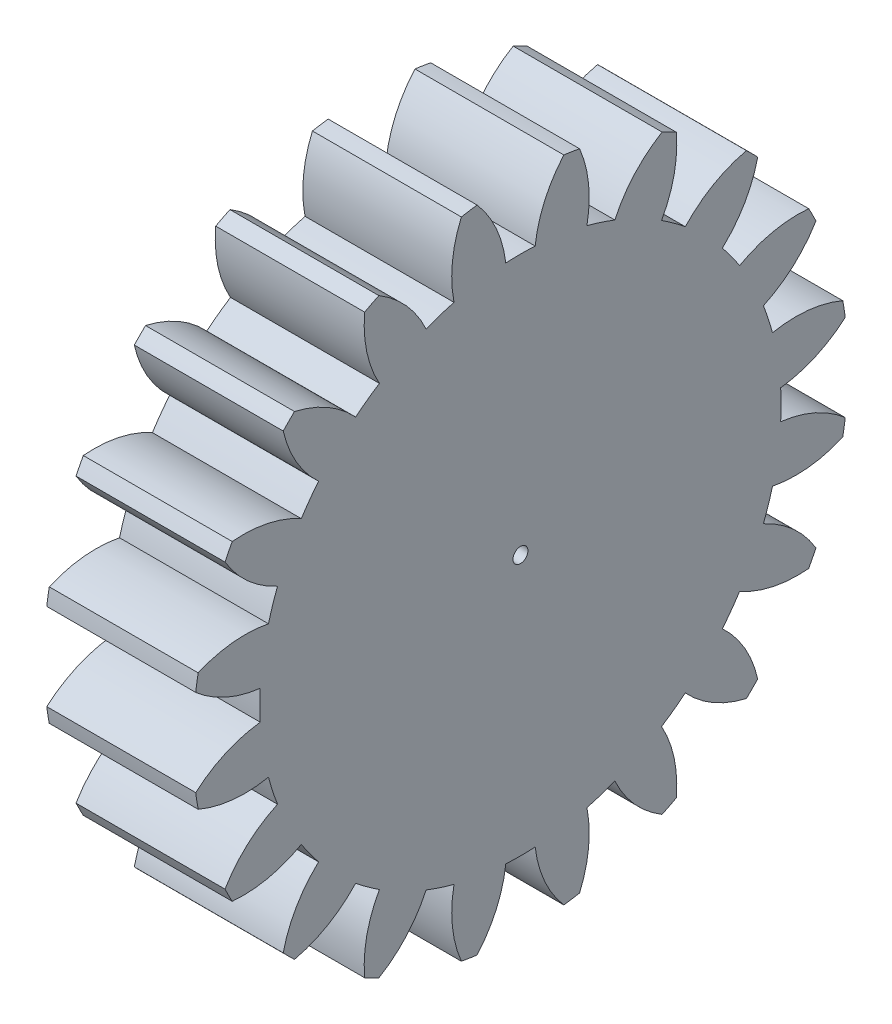
SolidWorks part; units mm, degrees
ref_plane "Plane1" through (0, 0, 0) normal (0, 0, 1) x (1, 0, 0)
ref_plane "Plane2" through (0, 0, 0) normal (0, 1, 0) x (1, 0, 0)
ref_plane "Plane3" through (0, 0, 0) normal (1, 0, 0) x (0, 0, -1)
other "Configuration Table"
sketch "HoldingSke" plane through (0, 0, 0) normal (0, 1, 0) x (1, 0, 0)
  line L0 (0, 0) -> (0.4698, -0.171)
  line L1 (-15, 0) -> (100, 0) construction
  line L2 (0, 0) -> (-2.1039, 2.3779)
  line L3 (0, 0) -> (-11.863, 4.5341)
  line L4 (0, 0) -> (8.1152, 2.9537)
  line L5 (0, 0) -> (-46.8476, -17.4728)
  line L6 (0, 0) -> (-8.2896, -5.593)
  line L7 (-2.1039, 2.3779) -> (8.6586, 51.2059)
  line L8 (-76.2, 54.61) -> (-76.1, 54.61)
  line L9 (-71.009, 38.7566) -> (-53.1078, 45.2721)
  line L10 (-76.2, 71.12) -> (104.1128, 71.12)
  line L11 (0, 0) -> (-10, 0)
  line L12 (-76.2, 101.6) -> (-76.133, 101.6)
  line L13 (24.9733, 27.94) -> (52.9518, 28.4284)
  line L14 (24.9733, 27.94) -> (24.9743, 27.94)
  line L15 (24.9733, 27.94) -> (100.4006, 29.5858)
  line L16 (-63.627, -2) -> (-12.827, -2)
  circle A0 centre (0, 0) radius 0.5
  circle A1 centre (0, 0) radius 17.499
  circle A2 centre (0, 0) radius 37.5
  circle A3 centre (0, 0) radius 0.5
  dimension "MHD" = 34.998
  dimension "Hub_dia" = 75
  dimension "Bore" = 1
  dimension "MBD" = 1
  dimension "Num_teeth" = 20
  dimension "Pitch" = 0.5
  dimension "Overall_len" = 50
  dimension "Show_teeth" = 20
  dimension "Thickness" = 10
  dimension "OAL" = 50.0001
  dimension "T_dim" = 0.1
  dimension "Ap" = 20
  dimension "H" = 19.05
  dimension "Pitch_radius" = 180.3128
  dimension "Width" = 10
  dimension "Backlash" = 0.067
  dimension "Addendum_fac" = 1
  dimension "Dedendum_fac" = 1.25
  dimension "Clearance_fac" = 0.25
  dimension "Dedendum_add" = 0.001
  dimension "Module" = 2
sketch "BasProSke" plane through (0, 0, 0) normal (0, 1, 0) x (1, 0, 0)
  line L0 (-10, 0) -> (60, 0) construction
  line L1 (0, 0) -> (0, 22)
  line L2 (0, 0) -> (10, 0)
  line L3 (10, 0) -> (10, 22)
  line L4 (10, 22) -> (0, 22)
  dimension "Thickness" = 10
  dimension "Diameter" = 44
revolve "Base-Revolve" add sketch "BasProSke" angle 360 about L0
sketch "TooCutSke" plane through (0, 0, 0) normal (1, 0, 0) x (0, 0, -1)
  line L1 (0, 0) -> (0, 107) construction
  line L2 (0, 0) -> (-1.6864, 19.9288) construction
  line L3 (0, 0) -> (-6.2409, 39.4033) construction
  line L4 (-1.6864, 19.9288) -> (-3.1204, 19.7016) construction
  arc A0 (0.9862, 17.4712) -> (-0.9862, 17.4712) centre (0, 0) ccw
  arc A1 (2.9329, 21.8293) -> (-2.9329, 21.8293) centre (0, 0) ccw
  circle A2 centre (0, 0) radius 20 construction
  circle A3 centre (0, 0) radius 18.7939 construction
  arc A4 (-0.9862, 17.4712) -> (-2.9329, 21.8293) centre (-8.9313, 16.536) ccw
  arc A5 (2.9329, 21.8293) -> (0.9862, 17.4712) centre (8.9313, 16.536) ccw
  dimension "Root_dia" = 34.998
  dimension "Overcut_dia" = 44.0508
  dimension "Pitch_dia" = 40
  dimension "Base_dia" = 37.5877
  dimension "Flank_rad" = 8
  dimension "Half_ang" = 9
  dimension "Half_CT" = 1.4519
extrude "ToothCut" cut sketch "TooCutSke" along normal through all
fillet "Breaks" [suppressed] radius 0.04
fillet "RootFillets" [suppressed] radius 0.501
pattern_circular "TeethCuts" count 20 every 18 about axis through (-10, 0, 0) along (1, 0, 0) of "ToothCut", "RootFillets", "Breaks"
sketch "HubNeaOneSke" plane through (0, 0, 0) normal (-1, 0, 0) x (0, 0, 1)
  circle A0 centre (0, 0) radius 17.499
  dimension "Diameter" = 34.998
extrude "HubNearOne" [suppressed] add sketch "HubNeaOneSke" along normal blind 40.0001
sketch "HubNeaBotSke" plane through (0, 0, 0) normal (-1, 0, 0) x (0, 0, 1)
  circle A0 centre (0, 0) radius 17.499
  dimension "Diameter" = 34.998
extrude "HubNearBoth" [suppressed] add sketch "HubNeaBotSke" along normal blind 20
ref_plane "FarPln" through (10, 0, 0) normal (1, 0, 0) x (0, 0, -1)
sketch "HubFarSke" plane through (10, 0, 0) normal (1, 0, 0) x (0, 0, -1)
  circle A0 centre (0, 0) radius 17.499
  dimension "Diameter" = 34.998
extrude "HubFar" [suppressed] add sketch "HubFarSke" along normal blind 20
sketch "BorSke" plane through (0, 0, 0) normal (1, 0, 0) x (0, 0, -1)
  circle A0 centre (0, 0) radius 0.5
  dimension "Diameter" = 1
extrude "Bore" cut sketch "BorSke" along normal mid plane 100.0001
sketch "KeySke" plane through (0, 0, 0) normal (1, 0, 0) x (0, 0, -1)
  line L0 (-0.05, 0) -> (-0.05, 0.6)
  line L1 (-0.05, 0.6) -> (0.05, 0.6)
  line L2 (0.05, 0.6) -> (0.05, 0)
  line L3 (0, 0) -> (0, 34) construction
  line L4 (-0.05, 0) -> (0.05, 0)
  dimension "Offset" = 0.6
  dimension "Width" = 0.1
extrude "Keyway" [suppressed] cut sketch "KeySke" along normal mid plane 100.0001
pattern_circular "Keyway2" [suppressed] count 2 every 90 about axis through (-10, 0, 0) along (1, 0, 0)
equation "' \"Module@HoldingSke\" = 6.35"
equation "' \"Num_teeth@HoldingSke\" = 12"
equation "' \"Ap@HoldingSke\" =  20"
equation "' \"Ap@HoldingSke\" = 20"
equation "' \"Width@HoldingSke\" = 0.5 * 25.4"
equation "' \"Hub_dia@HoldingSke\"= 1 * 25.4"
equation "' \"Hub_dia@HoldingSke\" = 1 * 25.4"
equation "' \"Overall_len@HoldingSke\" = 1.0 * 25.4"
equation "' \"Bore@HoldingSke\" = 0.75 * 25.4"
equation "' \"T_dim@HoldingSke\" = 0.1 * 25.4"
equation "' \"Width@KeySke\" = 0.25 * 25.4"
equation "' \"Show_teeth@HoldingSke\" = 13"
equation "' \"Backlash@HoldingSke\" = 0.009 * 25.4"
equation "' \"Addendum_fac@HoldingSke\" = 1.0"
equation "' \"Dedendum_fac@HoldingSke\" = 1.25"
equation "' \"Dedendum_add@HoldingSke\" = 0.00005 * 25.4"
equation "' \"Clearance_fac@HoldingSke\" = 0.25"
equation "\"Pitch@HoldingSke\" = 1 / \"Module@HoldingSke\""
equation "\"Overcut_dia@TooCutSke\" = (\"Num_teeth@HoldingSke\" + 2 * \"Addendum_fac@HoldingSke\") / \"Pitch@HoldingSke\" + 0.002 * 25.4"
equation "\"Pitch_dia@TooCutSke\" = \"Num_teeth@HoldingSke\" / \"Pitch@HoldingSke\""
equation "\"Base_dia@TooCutSke\" = \"Num_teeth@HoldingSke\" / \"Pitch@HoldingSke\" * cos((\"Ap@HoldingSke\"  * 3.14159265 / 180))"
equation "\"Root_dia@TooCutSke\" = (\"Num_teeth@HoldingSke\" + 2) / \"Pitch@HoldingSke\" - 2 * (\"Addendum_fac@HoldingSke\" + \"Dedendum_fac@HoldingSke\") / \"Pitch@HoldingSke\" - \"Dedendum_add@HoldingSke\" * 2"
equation "\"Half_ang@TooCutSke\" = 180 / \"Num_teeth@HoldingSke\""
equation "\"Half_CT@TooCutSke\" = \"Num_teeth@HoldingSke\" / \"Pitch@HoldingSke\" * sin((3.14159265 / 2 / \"Num_teeth@HoldingSke\")) / 2 - 7 * \"Backlash@HoldingSke\" / 4"
equation "\"Flank_rad@TooCutSke\" = \"Num_teeth@HoldingSke\" / \"Pitch@HoldingSke\" / 5"
equation "\"Radius@RootFillets\" = \"Clearance_fac@HoldingSke\" / \"Pitch@HoldingSke\" + \"Dedendum_add@HoldingSke\""
equation "\"Break_rad@Breaks\" = 0.02 / \"Pitch@HoldingSke\""
equation "\"Thickness@HoldingSke\" = \"Width@HoldingSke\""
equation "\"OAL@HoldingSke\" = \"Thickness@HoldingSke\""
equation "\"MHD@HoldingSke\" = (\"Num_teeth@HoldingSke\" + 2) / \"Pitch@HoldingSke\" - 2 * (\"Addendum_fac@HoldingSke\" + \"Dedendum_fac@HoldingSke\")  / \"Pitch@HoldingSke\" - \"Dedendum_add@HoldingSke\" * 2"
equation "\"MBD@HoldingSke\" = (\"Num_teeth@HoldingSke\" + 2) / \"Pitch@HoldingSke\" - 2 * (\"Addendum_fac@HoldingSke\" + \"Dedendum_fac@HoldingSke\")  / \"Pitch@HoldingSke\" - \"Dedendum_add@HoldingSke\" * 2 - 0.002 * 25.4"
equation "\"MHD@HoldingSke\" = ((sgn( \"MHD@HoldingSke\" - \"Hub_dia@HoldingSke\" )-1)*( \"MHD@HoldingSke\" - \"Hub_dia@HoldingSke\" ))/-2+ \"Hub_dia@HoldingSke\""
equation "\"MBD@HoldingSke\" = ((sgn( \"MBD@HoldingSke\" - \"Bore@HoldingSke\" )-1)*( \"MBD@HoldingSke\" - \"Bore@HoldingSke\" ))/-2+ \"Bore@HoldingSke\""
equation "\"OAL@HoldingSke\" = ((sgn( \"OAL@HoldingSke\" - \"Overall_len@HoldingSke\" )+1)*( \"OAL@HoldingSke\" - \"Overall_len@HoldingSke\" ))/2 + \"Overall_len@HoldingSke\" + 0.000002 * 25.4"
equation "\"Num_teeth@TeethCuts\" = int( \"Show_teeth@HoldingSke\" ) + 1"
equation "\"Num_teeth@TeethCuts\" = ((sgn( \"Num_teeth@TeethCuts\" - \"Num_teeth@HoldingSke\" )-1)*( \"Num_teeth@TeethCuts\" - \"Num_teeth@HoldingSke\" ))/-2+ \"Num_teeth@HoldingSke\""
equation "\"Num_teeth@TeethCuts\" = ((sgn( \"Num_teeth@TeethCuts\" - 2.0)+1)*( \"Num_teeth@TeethCuts\" - 2.0))/2 +2.0"
equation "\"Angle@TeethCuts\" = 360.0 / \"Num_teeth@HoldingSke\""
equation "\"Diameter@BasProSke\" = (\"Num_teeth@HoldingSke\" + 2 * \"Addendum_fac@HoldingSke\") / \"Pitch@HoldingSke\""
equation "\"Thickness@BasProSke\"  = \"Thickness@HoldingSke\""
equation "' \"Fillet_rad@BasProSke\" =  \"Thickness@HoldingSke\" * 0.05"
equation "' \"Fillet_rad@BasProSke\" = \"Thickness@HoldingSke\" * 0.05"
equation "\"MHD@HoldingSke\" = ((sgn( \"MHD@HoldingSke\" - \"Root_dia@TooCutSke\" )-1)*( \"MHD@HoldingSke\" - \"Root_dia@TooCutSke\" ))/-2+ \"Root_dia@TooCutSke\""
equation "\"Diameter@HubNeaOneSke\" = \"MHD@HoldingSke\""
equation "\"Length@HubNearOne\" = \"OAL@HoldingSke\" - \"Thickness@BasProSke\""
equation "\"Diameter@HubNeaBotSke\" = \"MHD@HoldingSke\""
equation "\"Length@HubNearBoth\" = ( \"OAL@HoldingSke\" - \"Thickness@BasProSke\" ) / 2.0"
equation "\"Thickness@FarPln\" = \"Thickness@BasProSke\""
equation "\"Diameter@HubFarSke\" = \"MHD@HoldingSke\""
equation "\"Length@HubFar\" = ( \"OAL@HoldingSke\" - \"Thickness@BasProSke\" ) / 2.0"
equation "\"Diameter@BorSke\" = \"MBD@HoldingSke\""
equation "\"D1@Bore\" = \"OAL@HoldingSke\" * 2.0"
equation "\"D1@Keyway\" = \"OAL@HoldingSke\" * 2.0"
equation "\"Offset@KeySke\" = \"T_dim@HoldingSke\" + \"MBD@HoldingSke\" / 2.0"
